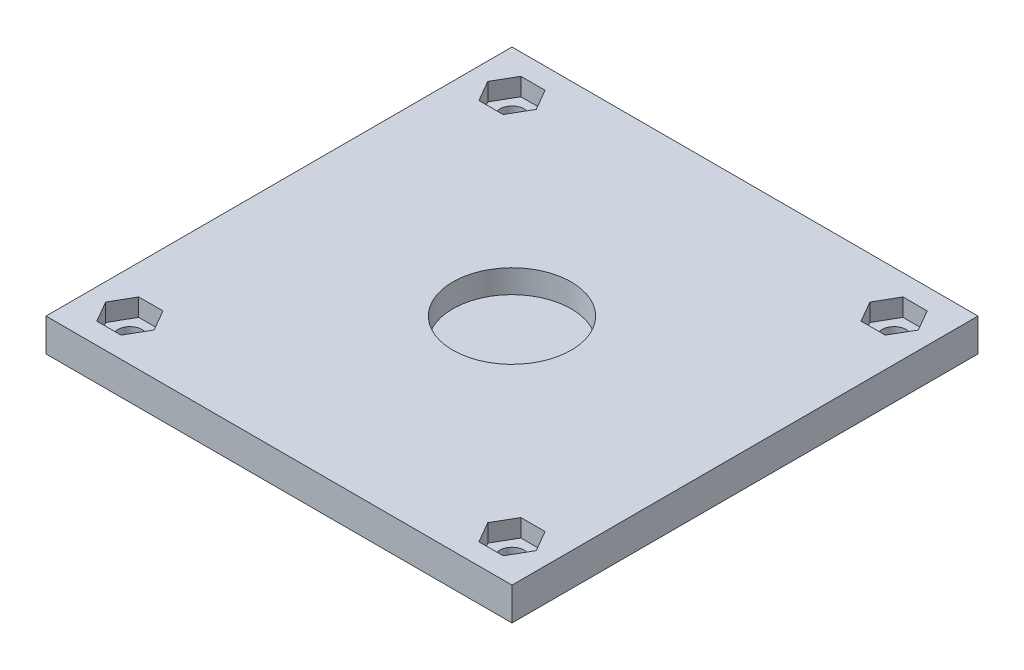
SolidWorks part; units mm, degrees
ref_plane "Front Plane" through (0, 0, 0) normal (0, 0, 1) x (1, 0, 0)
ref_plane "Top Plane" through (0, 0, 0) normal (0, 1, 0) x (1, 0, 0)
ref_plane "Right Plane" through (0, 0, 0) normal (1, 0, 0) x (0, 0, -1)
sketch "Sketch1" plane through (0, 0, 0) normal (0, 1, 0) x (1, 0, 0)
  line L0 (8.1304, -26.0013) -> (71.6304, -26.0013)
  line L1 (71.6304, 15.9087) -> (71.6304, -13.3013)
  line L2 (71.6304, -26.0013) -> (71.6304, -13.3013)
  line L3 (8.1304, -19.6513) -> (8.1304, 22.2587)
  line L4 (71.6304, 15.9087) -> (71.6304, 37.4987)
  line L5 (71.6304, 37.4987) -> (8.1304, 37.4987)
  line L6 (8.1304, 37.4987) -> (8.1304, 22.2587)
  line L7 (8.1304, -19.6513) -> (8.1304, -26.0013)
  point P6 (71.6304, -26.0013)
  point P9 (71.6304, 37.4987)
  point P12 (8.1304, -26.0013)
  dimension "D1" = 63.5
  dimension "D2" = 63.5
extrude "Boss-Extrude1" add sketch "Sketch1" along normal blind 4.476
sketch "Sketch2" plane through (0, 4.476, 0) normal (0, 1, 0) x (1, 0, 0)
  line L0 (71.6304, 37.4987) -> (8.1304, 37.4987) construction
  line L1 (64.2656, 28.9262) -> (67.5651, 28.9262)
  line L2 (17.1449, 31.7837) -> (15.4951, 34.6412)
  line L3 (67.5651, 28.9262) -> (69.2149, 31.7837)
  line L4 (15.4951, 34.6412) -> (12.1956, 34.6412)
  line L5 (8.1304, 37.4987) -> (8.1304, -26.0013) construction
  line L6 (8.1304, 37.4987) -> (8.1304, -26.0013)
  line L7 (12.1956, 34.6412) -> (10.5458, 31.7837)
  line L8 (62.6158, 31.7837) -> (64.2656, 28.9262)
  line L9 (64.2656, 34.6412) -> (62.6158, 31.7837)
  line L10 (67.5651, 34.6412) -> (64.2656, 34.6412)
  line L11 (69.2149, 31.7837) -> (67.5651, 34.6412)
  line L12 (64.2656, -23.1438) -> (67.5651, -23.1438)
  line L13 (67.5651, -23.1438) -> (69.2149, -20.2863)
  line L14 (62.6158, -20.2863) -> (64.2656, -23.1438)
  line L15 (64.2656, -17.4288) -> (62.6158, -20.2863)
  line L16 (67.5651, -17.4288) -> (64.2656, -17.4288)
  line L17 (69.2149, -20.2863) -> (67.5651, -17.4288)
  line L18 (12.1956, -23.1438) -> (15.4951, -23.1438)
  line L19 (15.4951, -23.1438) -> (17.1449, -20.2863)
  line L20 (10.5458, -20.2863) -> (12.1956, -23.1438)
  line L21 (12.1956, -17.4288) -> (10.5458, -20.2863)
  line L22 (15.4951, -17.4288) -> (12.1956, -17.4288)
  line L23 (17.1449, -20.2863) -> (15.4951, -17.4288)
  line L30 (10.5458, 31.7837) -> (12.1956, 28.9262)
  line L31 (12.1956, 28.9262) -> (15.4951, 28.9262)
  line L32 (15.4951, 28.9262) -> (17.1449, 31.7837)
  circle A0 centre (65.9154, 31.7837) radius 2.8575 construction
  circle A1 centre (65.9154, -20.2863) radius 2.8575 construction
  circle A2 centre (13.8454, -20.2863) radius 2.8575 construction
  circle A4 centre (13.8454, 31.7837) radius 2.8575 construction
  dimension "D2" = 2
  dimension "D4" = 5.715
  dimension "D1" = 2
  dimension "D5" = 5.715
  dimension "D6" = 5.715
extrude "Cut-Extrude1" cut sketch "Sketch2" against normal blind 2.413 contours L31 L32 L2 L4 L7 L30 | L3 L11 L10 L9 L8 L1 | L13 L17 L16 L15 L14 L12 | L19 L23 L22 L21 L20 L18
sketch "Sketch4" plane through (0, 4.476, 0) normal (0, 1, 0) x (1, 0, 0)
  line L0 (71.6304, 37.4987) -> (8.1304, 37.4987) construction
  line L1 (8.1304, 37.4987) -> (8.1304, -26.0013) construction
  circle A0 centre (65.9154, 31.7837) radius 1.65
  circle A1 centre (13.8454, 31.7837) radius 1.65
  circle A2 centre (65.9154, -20.2863) radius 1.65
  circle A3 centre (13.8454, -20.2863) radius 1.65
  dimension "D1" = 5.715
  dimension "D2" = 3.3
  dimension "D3" = 5.715
  dimension "D4" = 2
  dimension "D5" = 2
extrude "Cut-Extrude2" cut sketch "Sketch4" against normal through all
sketch "Sketch5" plane through (0, 4.476, 0) normal (0, 1, 0) x (1, 0, 0)
  line L0 (8.1304, -26.0013) -> (71.6304, -26.0013) construction
  line L1 (8.1304, -19.6513) -> (8.1304, 22.2587) construction
  circle A1 centre (39.8804, 5.7487) radius 8.0645
  dimension "D3" = 31.75
  dimension "D4" = 31.75
extrude "Cut-Extrude3" cut sketch "Sketch5" against normal blind 3.175
